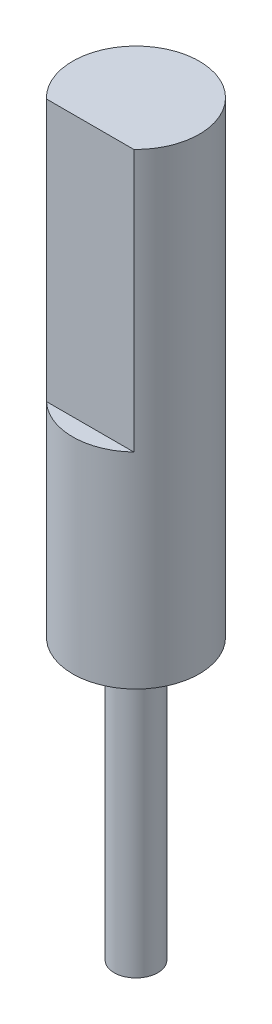
SolidWorks part; units mm, degrees
ref_plane "Alzado" through (0, 0, 0) normal (0, 0, 1) x (1, 0, 0)
ref_plane "Planta" through (0, 0, 0) normal (0, 1, 0) x (1, 0, 0)
ref_plane "Vista lateral" through (0, 0, 0) normal (1, 0, 0) x (0, 0, -1)
sketch "Croquis1" plane through (0, 0, 0) normal (0, 1, 0) x (1, 0, 0)
  circle A0 centre (0, 0) radius 1.45
  dimension "D1" = 2.9
extrude "Saliente-Extruir1" add sketch "Croquis1" along normal blind 10.7
sketch "Croquis2" plane through (0, 10.7, 0) normal (0, 1, 0) x (1, 0, 0)
  line L0 (-1, -1.05) -> (1, -1.05)
  arc A0 (-1, -1.05) -> (1, -1.05) centre (0, 0) ccw
  dimension "D1" = 1.05
extrude "Cortar-Extruir1" cut sketch "Croquis2" against normal blind 6
sketch "Croquis3" plane through (0, 0, 0) normal (0, -1, 0) x (1, 0, 0)
  circle A0 centre (0, 0) radius 0.5
  dimension "D1" = 1
extrude "Saliente-Extruir2" add sketch "Croquis3" along normal blind 6.4
